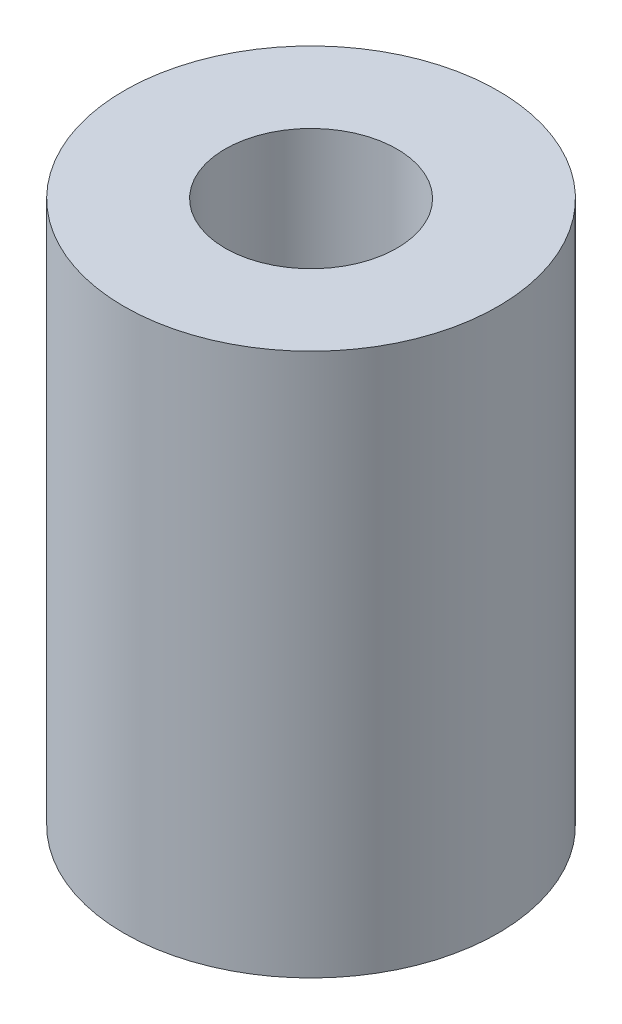
SolidWorks part; units mm, degrees
ref_plane "Front Plane" through (0, 0, 0) normal (0, 0, 1) x (1, 0, 0)
ref_plane "Top Plane" through (0, 0, 0) normal (0, 1, 0) x (1, 0, 0)
ref_plane "Right Plane" through (0, 0, 0) normal (1, 0, 0) x (0, 0, -1)
sketch "Sketch1" plane through (0, 0, 0) normal (0, 1, 0) x (1, 0, 0)
  circle A0 centre (0, 0) radius 1.425
  circle A1 centre (0, 0) radius 3.1
  dimension "D1" = 6.2
  dimension "D2" = 2.85
extrude "Boss-Extrude1" add sketch "Sketch1" along normal blind 9
sketch "Sketch2" [suppressed] plane through (0, 0, 0) normal (1, 0, 0) x (0, 0, -1)
  circle A0 centre (0, 0) radius 3.1
  circle A1 centre (0, 0) radius 1.5
  dimension "D1" = 6.2
  dimension "D2" = 3
extrude "Boss-Extrude2" [suppressed] add sketch "Sketch2" along normal blind 3
sketch "Sketch3" [suppressed] plane through (0, 0, 0) normal (0, 0, 1) x (1, 0, 0)
  circle A0 centre (0, 0) radius 3.1
  circle A1 centre (0, 0) radius 2
  dimension "D1" = 6.2
  dimension "D2" = 4
extrude "Boss-Extrude3" [suppressed] add sketch "Sketch3" along normal blind 1
sketch "Sketch4" [suppressed] plane through (0, 0, 0) normal (0, 0, 1) x (1, 0, 0)
  circle A0 centre (0, 0) radius 3.1
  circle A1 centre (0, 0) radius 2
  dimension "D1" = 6.2
  dimension "D2" = 4
extrude "Boss-Extrude4" [suppressed] add sketch "Sketch4" along normal blind 5
